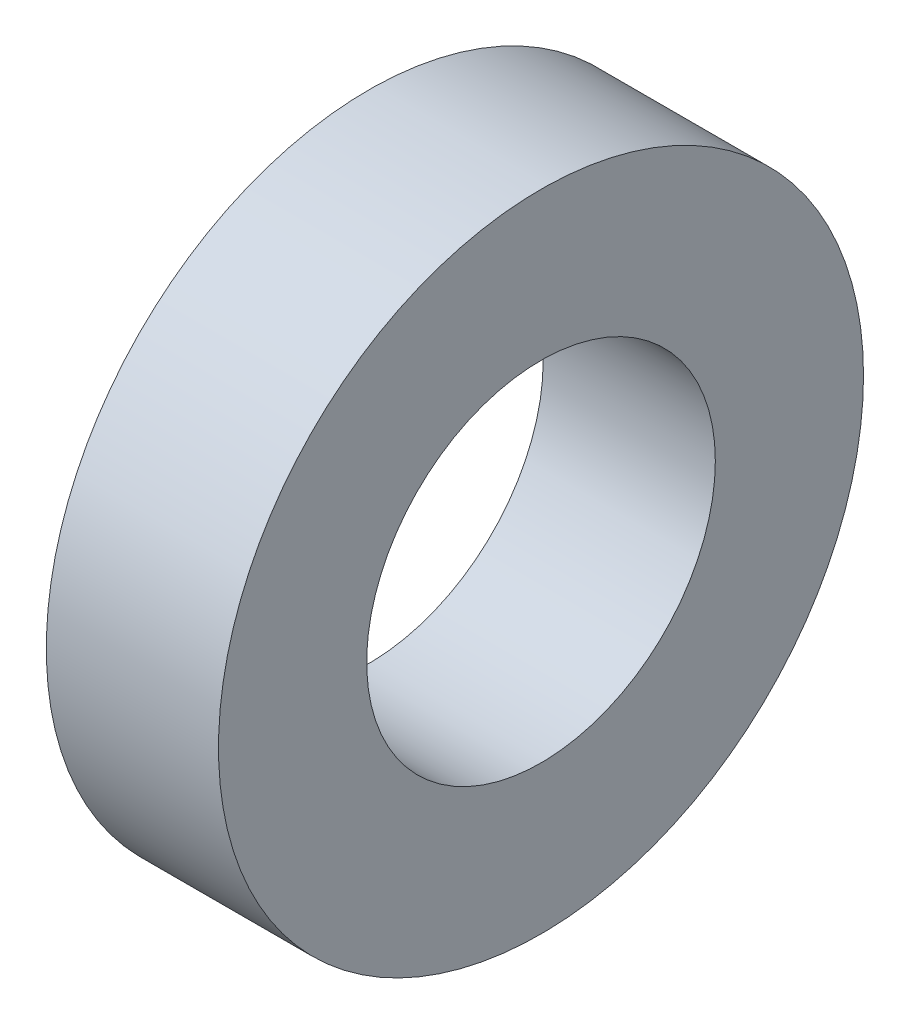
SolidWorks part; units mm, degrees
ref_plane "Front Plane" through (0, 0, 0) normal (0, 0, 1) x (1, 0, 0)
ref_plane "Top Plane" through (0, 0, 0) normal (0, 1, 0) x (1, 0, 0)
ref_plane "Right Plane" through (0, 0, 0) normal (1, 0, 0) x (0, 0, -1)
sketch "Sketch1" plane through (0, 0, 0) normal (1, 0, 0) x (0, 0, -1)
  circle A0 centre (0, 0) radius 15.875
  circle A1 centre (0, 0) radius 29.3688
  dimension "D1" = 31.75
  dimension "D2" = 58.7375
extrude "Boss-Extrude1" add sketch "Sketch1" along normal mid plane 15.68
